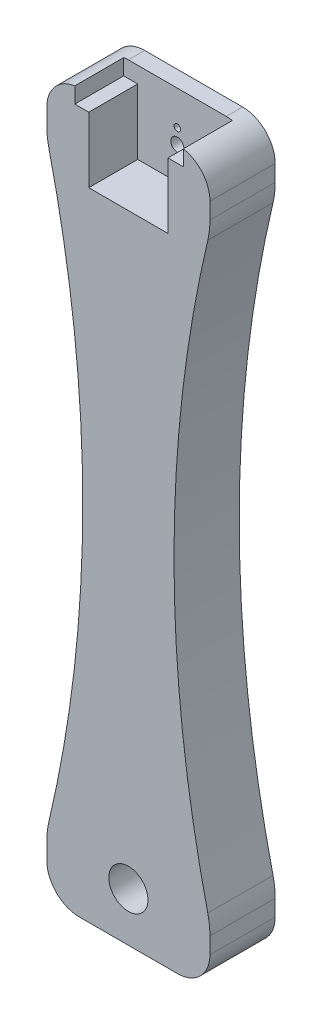
SolidWorks part; units mm, degrees
ref_plane "Front Plane" through (0, 0, 0) normal (0, 0, 1) x (1, 0, 0)
ref_plane "Top Plane" through (0, 0, 0) normal (0, 1, 0) x (1, 0, 0)
ref_plane "Right Plane" through (0, 0, 0) normal (1, 0, 0) x (0, 0, -1)
sketch "Sketch1" plane through (0, 0, 0) normal (0, 0, 1) x (1, 0, 0)
  line L1 (0, 0) -> (50, 0)
  line L2 (0, 0) -> (0, -220)
  line L3 (0, -220) -> (50, -220)
  line L4 (50, 0) -> (50, -220)
extrude "Boss-Extrude1" add sketch "Sketch1" along normal blind 20
sketch "Sketch2" plane through (0, 0, 20) normal (0, 0, 1) x (1, 0, 0)
  circle A1 centre (25, -15) radius 2
  circle A2 centre (25, -205) radius 6
extrude "Cut-Extrude2" cut sketch "Sketch2" against normal blind 34
fillet "Fillet2" radius 10 4 edges at (0, 0, 10) (50, 0, 10) (50, -220, 10) (0, -220, 10)
sketch "Sketch4" plane through (0, 0, 20) normal (0, 0, 1) x (1, 0, 0)
  line L1 (40, 0) -> (10, 0) construction
  line L3 (25, -25) -> (37.14, -25)
  line L4 (25, -25) -> (12.86, -25)
  line L5 (12.86, -25) -> (12.86, 0)
  line L6 (12.86, 0) -> (37.14, 0)
  line L7 (37.14, 0) -> (37.14, -25)
extrude "Cut-Extrude3" cut sketch "Sketch4" against normal blind 15
sketch "Sketch7" plane through (0, 0, 0) normal (0, 0, -1) x (-1, 0, 0)
  circle A0 centre (-25, -10.5) radius 1
  circle A1 centre (-25, -19.5) radius 1
extrude "Cut-Extrude4" cut sketch "Sketch7" against normal blind 15
sketch "Sketch8" plane through (0, 0, 20) normal (0, 0, 1) x (1, 0, 0)
  line L1 (37.14, -25) -> (37.14, 0) construction
  line L2 (37.14, -4.9564) -> (41.858, -4.9564)
  line L3 (12.86, -4.9564) -> (8.578, -4.9564)
  line L4 (12.86, 0) -> (12.86, -25) construction
  line L6 (8.578, -4.9564) -> (41.858, -4.9564)
  line L7 (8.578, -4.9564) -> (8.578, 3.1913)
  line L8 (8.578, 3.1913) -> (41.858, 3.1913)
  line L9 (41.858, -4.9564) -> (41.858, 3.1913)
  line M8 (37.14, 0) -> (37.14, -25)
  line M10 (12.86, -25) -> (12.86, 0)
  line M11 (12.86, 0) -> (10, 0)
  arc M12 (10, 0) -> (0, -10) centre (10, -10) ccw
  arc M18 (50, -10) -> (40, 0) centre (40, -10) ccw
  line M19 (40, 0) -> (37.14, 0)
extrude "Cut-Extrude6" cut sketch "Sketch8" against normal blind 15 contours L9 L8 L7 L6 M18 M12 M11 M10 M8 M19 | L7 L3 M10 M11 M12 | L2 L9 M18 M19 M8
sketch "Sketch9" plane through (0, 0, 20) normal (0, 0, 1) x (1, 0, 0)
  line L0 (50, -205) -> (50, -202.0544)
  line L1 (50, -210) -> (50, -10) construction
  line L2 (50, -205) -> (50, -15)
  line L3 (50, -10) -> (50, -205)
  line L4 (0, -205) -> (0, -19.137)
  line L5 (0.0042, -17.9627) -> (0, -15)
  arc A0 (0, -15) -> (0.6638, -20.7229) centre (25, -15) ccw
  arc A1 (0.6638, -199.2771) -> (0, -205) centre (25, -205) ccw
  arc A2 (0.6638, -199.2771) -> (0.6638, -20.7229) centre (-378.9802, -110) ccw
  arc A3 (49.3362, -20.7229) -> (49.3362, -199.2771) centre (428.9802, -110) ccw
  arc A4 (50, -205) -> (49.3362, -199.2771) centre (25, -205) ccw
  arc A5 (50, -10) -> (41.858, -0.1741) centre (40, -10) ccw construction
  arc A6 (49.3362, -20.7229) -> (50, -15) centre (25, -15) ccw
extrude "Cut-Extrude7" cut sketch "Sketch9" against normal blind 53
